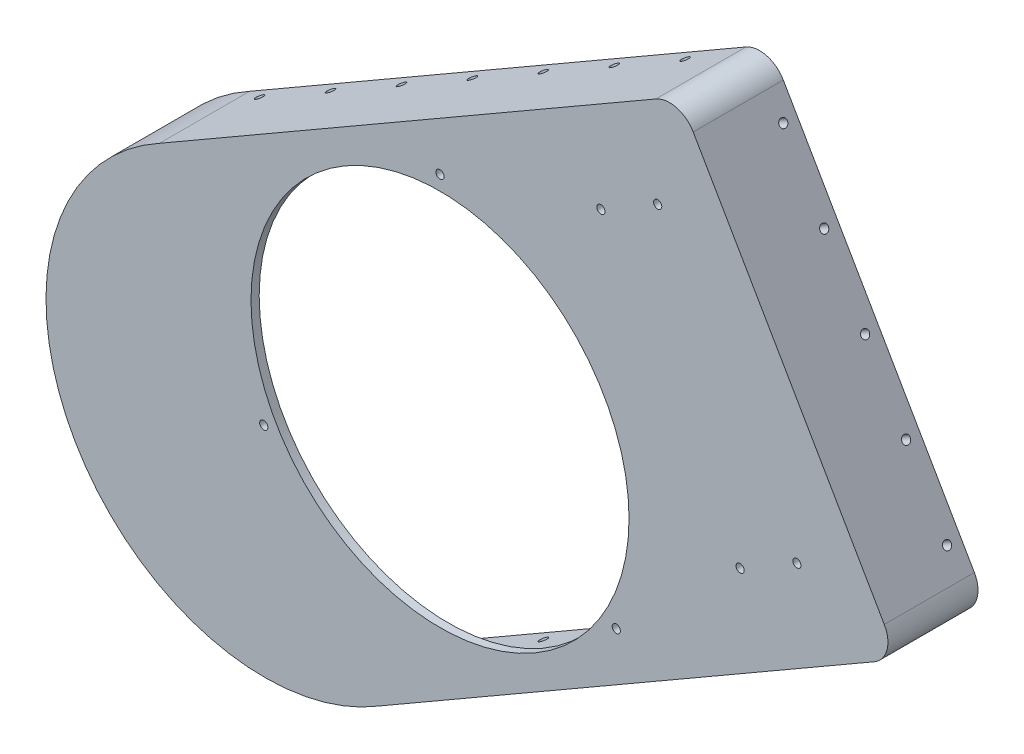
SolidWorks part; units mm, degrees
ref_plane "前视基准面" through (0, 0, 0) normal (0, 0, 1) x (1, 0, 0)
ref_plane "上视基准面" through (0, 0, 0) normal (0, 1, 0) x (1, 0, 0)
ref_plane "右视基准面" through (0, 0, 0) normal (1, 0, 0) x (0, 0, -1)
sketch "草图1" plane through (0, 0, 0) normal (0, 0, 1) x (1, 0, 0)
  line L0 (-133.6279, -77.1501) -> (127.7563, 73.7601) construction
  line L1 (-58.4567, -33.75) -> (-10.8429, -6.2601) construction
  line L4 (-22.7693, -105.5219) -> (96.8977, -36.4322)
  line L5 (-102.7693, 33.0422) -> (16.8977, 102.1319)
  line L6 (-2.9358, -1.695) -> (-52.5813, 84.2935) construction
  line L7 (92.7563, 134.3819) -> (162.7563, 13.1383)
  line L8 (16.8977, 102.1319) -> (79.096, 138.0422)
  line L9 (96.8977, -36.4322) -> (159.096, -0.5219)
  circle A0 centre (0, 74.5638) radius 1.5 construction
  circle A1 centre (64.5741, -37.2819) radius 1.5 construction
  circle A2 centre (-64.5741, -37.2819) radius 1.5 construction
  circle A3 centre (0, 74.5638) radius 1.5
  circle A4 centre (64.5741, -37.2819) radius 1.5
  circle A5 centre (-64.5741, -37.2819) radius 1.5
  arc A6 (-66.9209, -8.8231) -> (-41.1015, -53.5436) centre (0, 0) ccw construction
  circle A9 centre (0, 0) radius 69.25
  arc A12 (92.7563, 134.3819) -> (79.096, 138.0422) centre (84.096, 129.3819) ccw
  arc A13 (162.7563, 13.1383) -> (159.096, -0.5219) centre (154.096, 8.1383) cw
  arc A14 (-22.7693, -105.5219) -> (-102.7693, 33.0422) centre (-64.3284, -37.14) cw
  point P24 (-133.6279, -77.1501)
  point P32 (-93.6279, -146.4322)
  point P35 (-173.6279, -7.8681)
  point P44 (87.7563, 143.0422)
  point P45 (167.7563, 4.4781)
  point P46 (127.7563, 73.7601)
  dimension "D1" = 80
  dimension "D3" = 220
extrude "凸台-拉伸1" add sketch "草图1" along normal blind 3
sketch "草图2" plane through (0, 0, 0) normal (0, 0, -1) x (-1, 0, 0)
  line L0 (0, 0) -> (-127.7563, 73.7601) construction
  line L1 (-162.7563, 13.1383) -> (-92.7563, 134.3819) construction
  line L2 (-84.455, 48.7601) -> (-109.955, 4.5928) construction
  line L3 (-109.955, 4.5928) -> (-130.7396, 16.5928) construction
  circle A0 centre (-109.955, 4.5928) radius 1.5
  circle A1 centre (-130.7396, 16.5928) radius 1.5
  circle A2 centre (-58.955, 92.9274) radius 1.5
  circle A3 centre (-79.7396, 104.9274) radius 1.5
  dimension "D4" = 3
  dimension "D5" = 3
  dimension "D1" = 51
  dimension "D2" = 24
  dimension "D3" = 50
extrude "切除-拉伸1" cut sketch "草图2" against normal blind 10
sketch "草图20" plane through (0, 0, 0) normal (0, 0, -1) x (-1, 0, 0)
  line L0 (-89.2922, 132.3819) -> (-159.2922, 11.1383)
  line L1 (-157.096, 2.9422) -> (24.8088, -102.0806)
  line L2 (100.8088, 29.5553) -> (-81.096, 134.5781)
  line L3 (-92.7563, 134.3819) -> (-162.7563, 13.1383)
  line L4 (-159.096, -0.5219) -> (22.7693, -105.5219)
  line L5 (102.7693, 33.0422) -> (-79.096, 138.0422)
  line L6 (-92.7563, 134.3819) -> (-162.7563, 13.1383)
  line L7 (-159.096, -0.5219) -> (22.7693, -105.5219)
  line L8 (102.7693, 33.0422) -> (-79.096, 138.0422)
  arc A0 (-81.096, 134.5781) -> (-89.2922, 132.3819) centre (-84.096, 129.3819) ccw
  arc A1 (-159.2922, 11.1383) -> (-157.096, 2.9422) centre (-154.096, 8.1383) ccw
  arc A2 (24.8088, -102.0806) -> (100.8088, 29.5553) centre (64.3284, -37.14) ccw
  arc A3 (-79.096, 138.0422) -> (-92.7563, 134.3819) centre (-84.096, 129.3819) ccw
  arc A4 (-162.7563, 13.1383) -> (-159.096, -0.5219) centre (-154.096, 8.1383) ccw
  arc A5 (22.7693, -105.5219) -> (102.7693, 33.0422) centre (64.3284, -37.14) ccw
  arc A6 (-79.096, 138.0422) -> (-92.7563, 134.3819) centre (-84.096, 129.3819) ccw
  arc A7 (-162.7563, 13.1383) -> (-159.096, -0.5219) centre (-154.096, 8.1383) ccw
  arc A8 (22.7693, -105.5219) -> (102.7693, 33.0422) centre (64.3284, -37.14) ccw
  dimension "D1" = 0
  dimension "D2" = 4
extrude "凸台-拉伸4" add sketch "草图20" along normal blind 30
sketch "草图21" plane through (-40, 69.282, 0) normal (-0.5, 0.866, 0) x (0.866, 0.5, 0)
  line L1 (-72.4797, -3) -> (-72.4797, 30) construction
  line L2 (-72.4797, 30) -> (137.5203, 30) construction
  circle A0 centre (-62.4797, 25) radius 1.5
  circle A1 centre (-32.4797, 25) radius 1.5
  circle A2 centre (-2.4797, 25) radius 1.5
  circle A3 centre (27.5203, 25) radius 1.5
  circle A4 centre (57.5203, 25) radius 1.5
  circle A5 centre (87.5203, 25) radius 1.5
  circle A6 centre (117.5203, 25) radius 1.5
  dimension "D1" = 3
  dimension "D2" = 5
  dimension "D3" = 10
  dimension "D4" = 7
extrude "切除-拉伸16" cut sketch "草图21" against normal through all
sketch "草图22" plane through (127.7563, 73.7601, 0) normal (0.866, 0.5, 0) x (0, 0, -1)
  line L0 (30, 70) -> (30, -70) construction
  line L1 (-3, 70) -> (30, 70) construction
  circle A0 centre (25, 60) radius 1.5
  circle A1 centre (25, 30) radius 1.5
  circle A2 centre (25, 0) radius 1.5
  circle A3 centre (25, -30) radius 1.5
  circle A4 centre (25, -60) radius 1.5
  dimension "D1" = 3
  dimension "D2" = 5
  dimension "D3" = 10
  dimension "D4" = 5
extrude "切除-拉伸17" cut sketch "草图22" against normal blind 15
